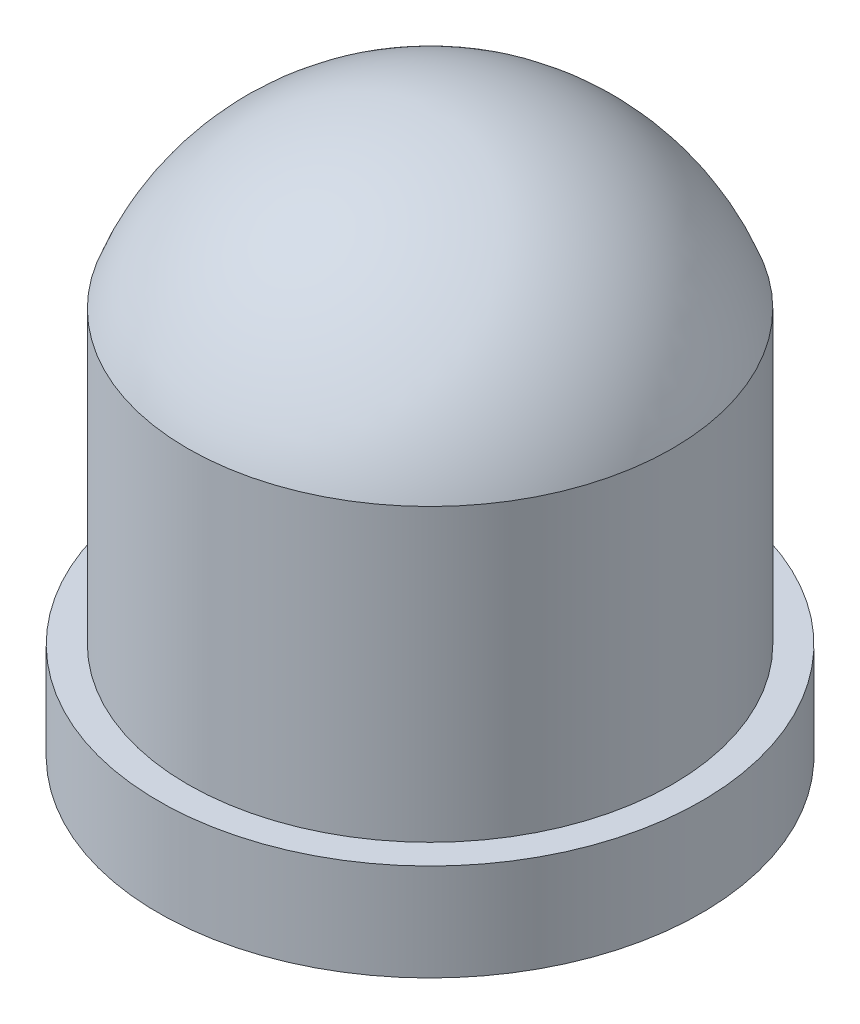
SolidWorks part; units mm, degrees
material "Acrylic (Medium-high impact)"
ref_plane "Front Plane" through (0, 0, 0) normal (0, 0, 1) x (1, 0, 0)
ref_plane "Top Plane" through (0, 0, 0) normal (0, 1, 0) x (1, 0, 0)
ref_plane "Right Plane" through (0, 0, 0) normal (1, 0, 0) x (0, 0, -1)
sketch "Sketch1" plane through (0, 0, 0) normal (1, 0, 0) x (0, 0, -1)
  line L0 (0, 0) -> (5.6, 0)
  line L1 (5.6, 0) -> (5.6, 2)
  line L2 (5.6, 2) -> (5, 2)
  line L3 (5, 2) -> (5, 8)
  line L4 (0, 0) -> (0, 11.5) construction
  line L5 (0, 0) -> (0, 11.5)
  arc A0 (5, 8) -> (0, 11.5) centre (0, 6.1786) ccw
  dimension "D1" = 10
  dimension "D2" = 11.2
  dimension "D3" = 11.5
  dimension "D4" = 2
  dimension "D5" = 6
revolve "Revolve1" add sketch "Sketch1" angle 360 about L4
